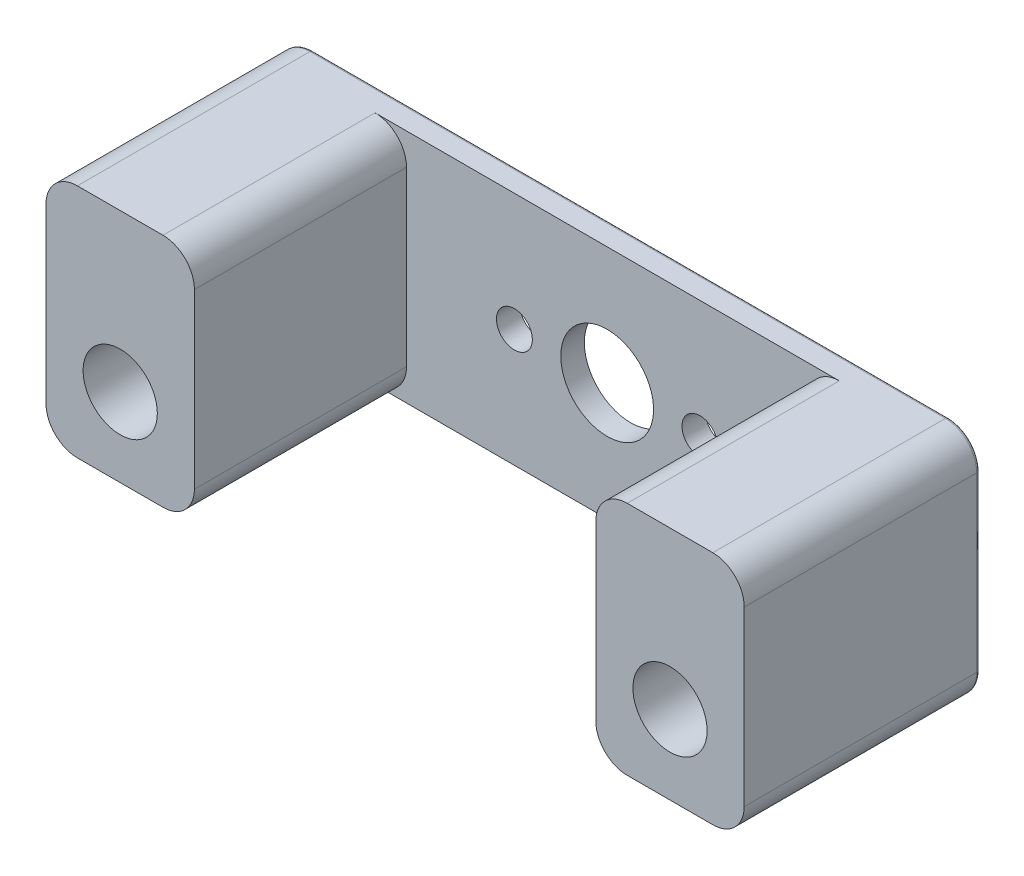
SolidWorks part; units mm, degrees
ref_plane "Front Plane" through (0, 0, 0) normal (0, 0, 1) x (1, 0, 0)
ref_plane "Top Plane" through (0, 0, 0) normal (0, 1, 0) x (1, 0, 0)
ref_plane "Right Plane" through (0, 0, 0) normal (1, 0, 0) x (0, 0, -1)
sketch "Sketch1" plane through (0, 0, 0) normal (0, 0, 1) x (1, 0, 0)
  line L1 (-28.2245, 9.525) -> (28.2245, 9.525)
  line L2 (-28.2245, 9.525) -> (-28.2245, -9.525)
  line L3 (-28.2245, -9.525) -> (28.2245, -9.525)
  line L4 (28.2245, 9.525) -> (28.2245, -9.525)
  line L5 (-28.2245, 9.525) -> (28.2245, -9.525) construction
  line L6 (-28.2245, -9.525) -> (28.2245, 9.525) construction
  line L7 (-28.2245, -9.525) -> (37.8155, -9.525)
  line L11 (0, -9.525) -> (0, 9.525) construction
  circle A0 centre (0, 0) radius 4.7625
  circle A1 centre (-22.225, -3.175) radius 2.9997
  circle A3 centre (22.225, -3.175) radius 2.9997
  point P0 (0, 0)
  point P10 (0, 0)
  dimension "D3" = 9.525
  dimension "D4" = 5.9995
  dimension "D1" = 19.05
  dimension "D2" = 44.45
  dimension "D5" = 12.7
  dimension "D6" = 5.9995
extrude "Boss-Extrude1" add sketch "Sketch1" along normal blind 19.05
sketch "Sketch2" plane through (0, 0, 0) normal (0, 0, -1) x (-1, 0, 0)
  line L0 (0, 7.5) -> (0, -7.5)
  line L1 (-7.5, 0) -> (7.5, 0)
  circle A0 centre (-7.5, 0) radius 1.45
  circle A1 centre (0, -7.5) radius 1.45
  circle A2 centre (7.5, 0) radius 1.45
  circle A3 centre (0, 0) radius 3.75
  circle A4 centre (0, 7.5) radius 1.45
  point P11 (0, 0)
  point P12 (0, 0)
  dimension "D3" = 2.9
  dimension "D4" = 2.9
  dimension "D5" = 2.9
  dimension "D6" = 2.9
  dimension "D7" = 7.5
  dimension "D1" = 15
  dimension "D2" = 15
extrude "Cut-Extrude1" cut sketch "Sketch2" against normal up to surface (19.05 mm away) up to face at (0, 0, 19.05)
sketch "Sketch3" plane through (0, 9.525, 0) normal (0, 1, 0) x (1, 0, 0)
  line L0 (25.2247, 0) -> (19.2253, 0) construction
  line L1 (-19.2253, 0) -> (-25.2247, 0) construction
  line L5 (25.2247, 0) -> (19.2253, 0)
  line L6 (-19.2253, 0) -> (-25.2247, 0)
  line L8 (16.2255, 0) -> (-16.2255, 0)
  line L10 (16.2255, -1.905) -> (-16.2255, -1.905)
  line L11 (16.2255, -19.05) -> (-16.2255, -19.05)
  line L13 (-19.2253, 0) -> (-19.2253, -19.05) construction
  line L14 (19.2253, 0) -> (19.2253, -19.05) construction
  line L15 (16.2255, 0) -> (16.2255, -19.05)
  line L16 (-16.2255, 0) -> (-16.2255, -19.05)
  line M6 (-28.2245, -19.05) -> (28.2245, -19.05)
  dimension "D1" = 2.9997
  dimension "D3" = 1.905
  dimension "D2" = 2.9997
extrude "Cut-Extrude2" cut sketch "Sketch3" against normal up to surface (19.05 mm away) contours L10 L16 L15 M6 up to face at (0, -9.525, 9.525)
fillet "Fillet1" radius 2.54 8 edges at (28.2245, -9.525, 9.525) (-28.2245, -9.525, 9.525) (-16.2255, -9.525, 10.4775) (16.2255, -9.525, 10.4775) (16.2255, 9.525, 10.4775) (-16.2255, 9.525, 10.4775) (28.2245, 9.525, 9.525) (-28.2245, 9.525, 9.525)
fillet "Fillet3" radius 0.254 8 edges at (-27.4805, 8.7811, 0) (-28.2245, 0, 0) (-27.4805, -8.7811, 0) (0, -9.525, 0) (27.4805, -8.7811, 0) (28.2245, 0, 0) (27.4805, 8.7811, 0) (0, 9.525, 0)
